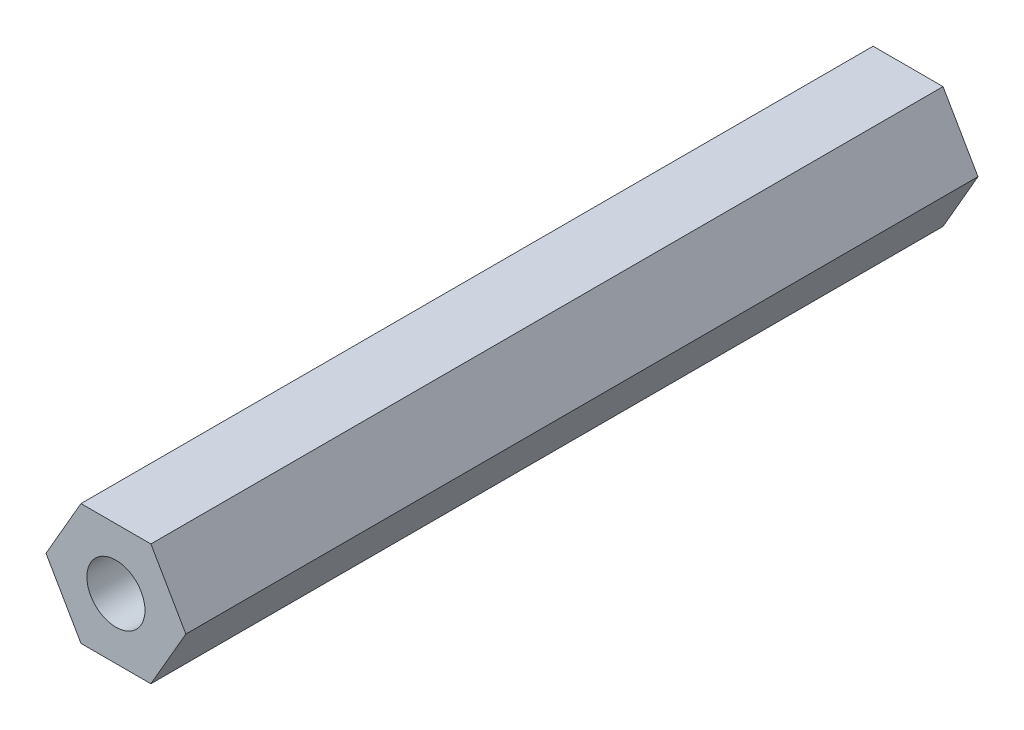
SolidWorks part; units mm, degrees
material "AISI 304"
ref_plane "前视基准面" through (0, 0, 0) normal (0, 0, 1) x (1, 0, 0)
ref_plane "上视基准面" through (0, 0, 0) normal (0, 1, 0) x (1, 0, 0)
ref_plane "右视基准面" through (0, 0, 0) normal (1, 0, 0) x (0, 0, -1)
sketch "草图1" plane through (0, 0, 0) normal (0, 0, 1) x (1, 0, 0)
  line L1 (1.9861, 3.44) -> (-1.9861, 3.44)
  line L2 (-1.9861, 3.44) -> (-3.9722, 0)
  line L3 (-3.9722, 0) -> (-1.9861, -3.44)
  line L4 (-1.9861, -3.44) -> (1.9861, -3.44)
  line L5 (1.9861, -3.44) -> (3.9722, 0)
  line L6 (3.9722, 0) -> (1.9861, 3.44)
  circle A0 centre (0, 0) radius 3.44 construction
  dimension "六角对边长度" = 6.88
extrude "六角柱长度" add sketch "草图1" along normal mid plane 45
hole_wizard "螺纹孔1" positions "草图2" profile "草图3" tap size "M2" standard "GB"
sketch "草图2" plane through (0, 0, 22.5) normal (0, 0, 1) x (1, 0, 0)
  point P0 (0, 0)
cosmetic thread "孔螺蚊线1"
sketch "草图3" plane through (0, 0, 22.5) normal (1, 0, 0) x (0, -1, 0)
  line L0 (0, 0) -> (0, 14.1914)
  line L1 (0, 14.1914) -> (1.65, 13.2)
  line L2 (1.65, 13.2) -> (1.65, 0)
  line L5 (1.65, 0) -> (0, 0)
  line L10 (0, 14.1914) -> (-1.65, 13.2) construction
  line L11 (0, -6.35) -> (0, 107.95) construction
  dimension "螺纹孔钻头直径" = 3.3
  dimension "螺纹孔钻头深度" = 13.2
  dimension "导头角度" = 118
mirror "镜向1" about plane through (0, 0, 0) normal (0, 0, 1) of "螺纹孔1"
cosmetic thread "孔螺蚊线2" parameters "D1"=12, "D2"=3.6
